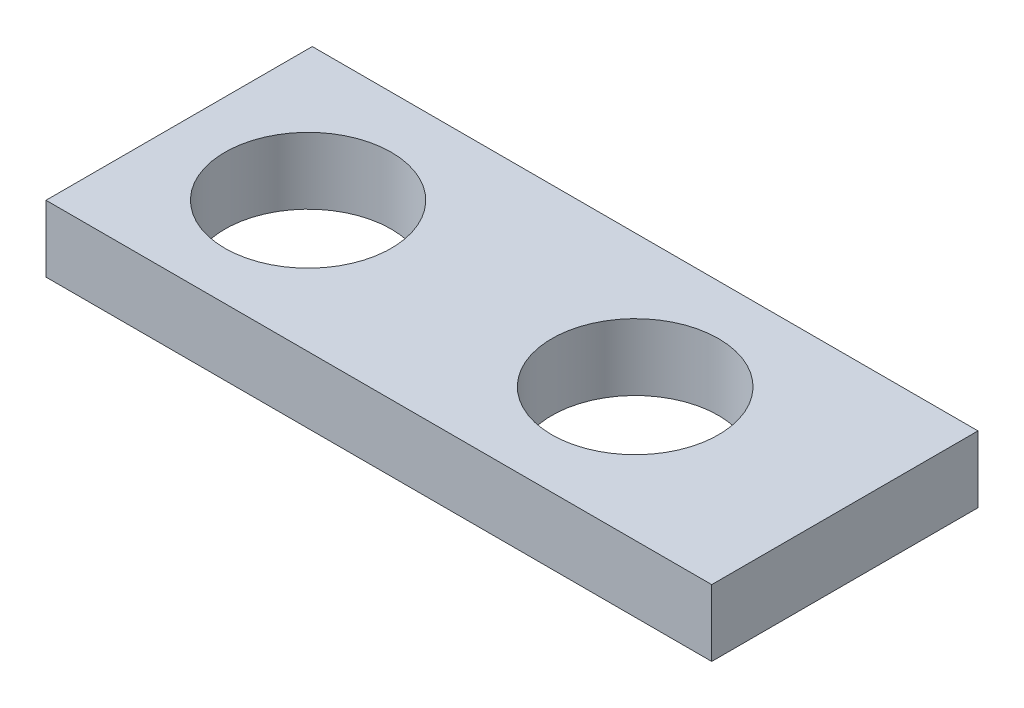
SolidWorks part; units mm, degrees
ref_plane "Front Plane" through (0, 0, 0) normal (0, 0, 1) x (1, 0, 0)
ref_plane "Top Plane" through (0, 0, 0) normal (0, 1, 0) x (1, 0, 0)
ref_plane "Right Plane" through (0, 0, 0) normal (1, 0, 0) x (0, 0, -1)
sketch "Sketch1" plane through (0, 0, 0) normal (0, 1, 0) x (1, 0, 0)
  line L1 (0, 0) -> (127, 0)
  line L2 (0, 0) -> (0, 50.8)
  line L3 (0, 50.8) -> (127, 50.8)
  line L4 (127, 0) -> (127, 50.8)
  dimension "D1" = 127
  dimension "D2" = 50.8
extrude "Boss-Extrude1" add sketch "Sketch1" along normal blind 12.7
sketch "Sketch2" plane through (0, 12.7, 0) normal (0, 1, 0) x (1, 0, 0)
  line L1 (0, 0) -> (25, 0)
  line L2 (0, 0) -> (0, 25)
  line L3 (0, 25) -> (25, 25)
  line L4 (25, 0) -> (25, 25)
  circle A0 centre (25, 25) radius 15.875
  dimension "D1" = 25
  dimension "D2" = 25
extrude "Cut-Extrude1" cut sketch "Sketch2" against normal blind 12.7 contours L4 A0 L3 | L3 A0 L4
sketch "Sketch4" plane through (0, 12.7, 0) normal (0, 1, 0) x (1, 0, 0)
  line L1 (0, 0) -> (87, 0)
  line L2 (0, 0) -> (0, 25.4)
  line L3 (0, 25.4) -> (87, 25.4)
  line L4 (87, 0) -> (87, 25.4)
  circle A0 centre (87, 25.4) radius 15.9
  dimension "D1" = 25.4
  dimension "D2" = 87
extrude "Cut-Extrude2" cut sketch "Sketch4" against normal through all contours L4 A0 L3 | L3 A0 L4
